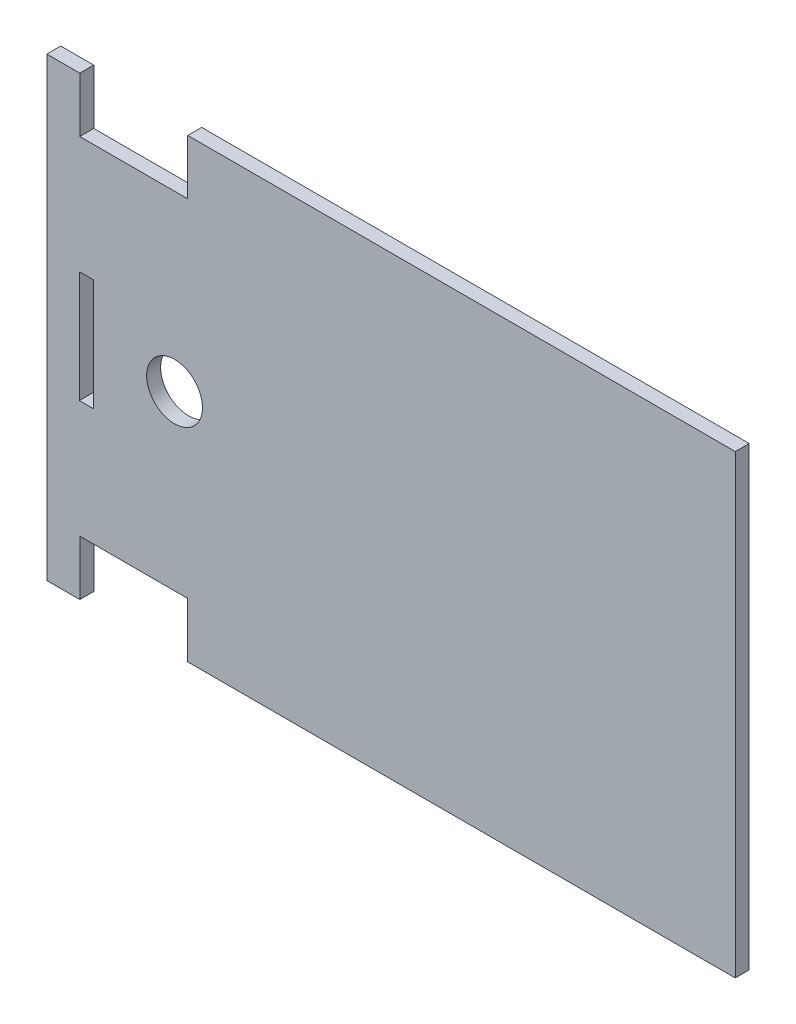
SolidWorks part; units mm, degrees
ref_plane "Alzado" through (0, 0, 0) normal (0, 0, 1) x (1, 0, 0)
ref_plane "Planta" through (0, 0, 0) normal (0, 1, 0) x (1, 0, 0)
ref_plane "Vista lateral" through (0, 0, 0) normal (1, 0, 0) x (0, 0, -1)
sketch "Model" plane through (0, 0, 0) normal (0, 0, 1) x (1, 0, 0)
  line L1 (-39.5113, -9.1851) -> (-32.4113, -9.1851)
  line L2 (50.5172, -9.1851) -> (78.4887, -9.1851)
  line L3 (96.4887, -9.1851) -> (103.4887, -9.1851)
  line L4 (78.4887, -9.1851) -> (89.4887, -9.1851)
  line L5 (89.4887, -9.1851) -> (96.4887, -9.1851)
  line L6 (-1.5113, 88.8149) -> (-0.5113, 88.8149)
  line L7 (-0.5113, 88.8149) -> (2.2887, 88.8149)
  line L8 (2.2887, 88.8149) -> (24.4887, 88.8149)
  line L9 (24.4887, 88.8149) -> (108.4887, 88.8149)
  line L10 (108.4887, 88.8149) -> (108.4887, -9.1851)
  line L11 (108.4887, -9.1851) -> (103.4887, -9.1851)
  line L13 (-32.4113, 2.6149) -> (-32.4113, -9.1851)
  line L14 (-9.2113, 2.6149) -> (-32.4113, 2.6149)
  line L15 (-9.2113, -9.1851) -> (-9.2113, 2.6149)
  line L16 (-9.2113, 88.8149) -> (-1.5113, 88.8149)
  line L17 (-9.2113, 77.0149) -> (-9.2113, 88.8149)
  line L18 (-32.4113, 77.0149) -> (-9.2113, 77.0149)
  line L19 (-32.4113, 88.8149) -> (-32.4113, 77.0149)
  line L20 (-39.5113, 88.8149) -> (-32.4113, 88.8149)
  line L21 (-39.5113, -9.1851) -> (-39.5113, 88.8149)
  line L22 (-29.5113, 51.8149) -> (-32.5113, 51.8149)
  line L23 (-32.5113, 51.8149) -> (-32.5113, 27.8149)
  line L24 (-32.5113, 27.8149) -> (-29.5113, 27.8149)
  line L25 (-29.5113, 27.8149) -> (-29.5113, 51.8149)
  line L26 (-9.2113, -9.1851) -> (16.002, -9.1851)
  line L27 (16.002, -9.1851) -> (50.5172, -9.1851)
  circle A0 centre (-12.0408, 39.7142) radius 6
extrude "Saliente-Extruir2" add sketch "Model" along normal blind 3
